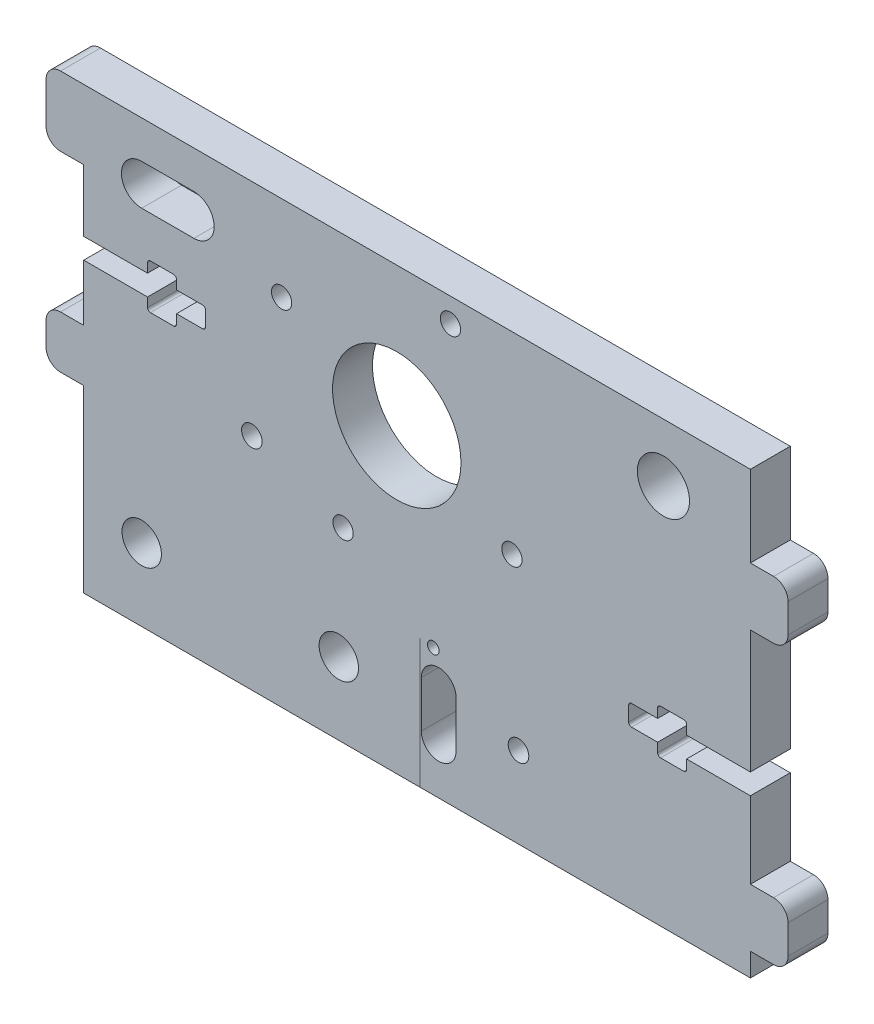
SolidWorks part; units mm, degrees
material "Melamine resin"
ref_plane "Front Plane" through (0, 0, 0) normal (0, 0, 1) x (1, 0, 0)
ref_plane "Top Plane" through (0, 0, 0) normal (0, 1, 0) x (1, 0, 0)
ref_plane "Right Plane" through (0, 0, 0) normal (1, 0, 0) x (0, 0, -1)
sketch "Sketch1" plane through (0, 0, 0) normal (0, 0, 1) x (1, 0, 0)
  line L1 (57.5, 38) -> (-57.5, 38)
  line L2 (57.5, 38) -> (57.5, -38)
  line L3 (57.5, -38) -> (-57.5, -38)
  line L4 (-57.5, 38) -> (-57.5, -38)
  line L5 (57.5, 38) -> (-57.5, -38) construction
  line L6 (57.5, -38) -> (-57.5, 38) construction
  line L7 (5.7639, 33.8665) -> (-23.3665, 23.2639) construction
  line L8 (5.7639, 33.8665) -> (16.3665, 4.7361) construction
  line L9 (16.3665, 4.7361) -> (-12.7639, -5.8665) construction
  line L10 (-23.3665, 23.2639) -> (-12.7639, -5.8665) construction
  line L11 (5.7639, 33.8665) -> (-12.7639, -5.8665) construction
  line L12 (16.3665, 4.7361) -> (-23.3665, 23.2639) construction
  circle A0 centre (-23.3665, 23.2639) radius 1.75
  circle A1 centre (-3.5, 14) radius 11.075
  circle A2 centre (5.7639, 33.8665) radius 1.75
  circle A3 centre (16.3665, 4.7361) radius 1.75
  circle A4 centre (-12.7639, -5.8665) radius 1.75
  point P0 (0, 0)
  point P5 (-3.5, 14)
  dimension "D1" = 31
  dimension "D2" = 3.5
  dimension "D3" = 22.15
  dimension "D7" = 52
  dimension "D6" = 54
  dimension "D4" = 115
  dimension "D5" = 76
  dimension "D8" = 20
extrude "Boss-Extrude1" add sketch "Sketch1" along normal blind 6.88
sketch "Sketch2" plane through (0, 0, 6.88) normal (0, 0, 1) x (1, 0, 0)
  line L0 (-47.5, -25.5) -> (-13.5, -25.5) construction
  line L1 (-57.5, -38) -> (57.5, -38) construction
  line L2 (-57.5, 38) -> (-57.5, -38) construction
  circle A0 centre (-47.5, -25.5) radius 3.4
  circle A1 centre (-13.5, -25.5) radius 3.4
  dimension "D1" = 6.8
  dimension "D4" = 10
  dimension "D2" = 12.5
  dimension "D3" = 34
extrude "Cut-Extrude1" cut sketch "Sketch2" against normal through all
sketch "Sketch4" plane through (0, 0, 6.88) normal (0, 0, 1) x (1, 0, 0)
  line L0 (-47.5, -25.5) -> (-66.0382, -25.5) construction
  line L1 (-66.0382, 2.9858) -> (-22.2006, 2.9858) construction
  circle A0 centre (17.5, -24) radius 1.775
  circle A1 centre (17.5, -24) radius 12.7 construction
  circle A3 centre (-28.5, 0) radius 1.775
  circle A4 centre (-13.5, -25.5) radius 3.4 construction
  dimension "D1" = 3.55
  dimension "D2" = 25.4
  dimension "D4" = 24
  dimension "D6" = 1.5
  dimension "D3" = 31
  dimension "D5" = 46
extrude "Cut-Extrude3" cut sketch "Sketch4" against normal through all
sketch "Sketch6" plane through (0, 0, 6.88) normal (0, 0, 1) x (1, 0, 0)
  line L0 (57.5, -38) -> (57.5, 38) construction
  line L1 (51, 14) -> (64, 14)
  line L2 (51, 14) -> (51, 24)
  line L3 (51, 24) -> (64, 24)
  line L4 (64, 14) -> (64, 24)
  line L5 (51, 14) -> (64, 24) construction
  line L6 (51, 24) -> (64, 14) construction
  line L7 (-57.5, -38) -> (57.5, -38) construction
  line L9 (45, -34) -> (64, -34)
  line L10 (45, -34) -> (45, -24)
  line L11 (45, -24) -> (64, -24)
  line L12 (64, -34) -> (64, -24)
  point P0 (57.5, 19)
  dimension "D1" = 6.5
  dimension "D2" = 10
  dimension "D4" = 10
  dimension "D5" = 4
extrude "Boss-Extrude2" add sketch "Sketch6" against normal up to surface (6.88 mm away) up to face at (-26.725, 0, 0)
sketch "Sketch7" plane through (0, 0, 6.88) normal (0, 0, 1) x (1, 0, 0)
  line L0 (57.5, 24) -> (57.5, 38) construction
  line L1 (78.5, -10.775) -> (36.5, -10.775)
  line L2 (78.5, -10.775) -> (78.5, -7.225)
  line L3 (78.5, -7.225) -> (36.5, -7.225)
  line L4 (36.5, -10.775) -> (36.5, -7.225)
  line L5 (78.5, -10.775) -> (36.5, -7.225) construction
  line L6 (78.5, -7.225) -> (36.5, -10.775) construction
  line L7 (57.5, -38) -> (57.5, -34) construction
  line L8 (-57.5, -38) -> (57.5, -38) construction
  point P0 (57.5, -9)
  dimension "D1" = 3.55
  dimension "D2" = 21
  dimension "D3" = 29
extrude "Cut-Extrude4" cut sketch "Sketch7" against normal through all
sketch "Sketch8" plane through (0, 0, 6.88) normal (0, 0, 1) x (1, 0, 0)
  line L0 (36.5, -9) -> (44, -9) construction
  line L1 (36.5, -7.225) -> (36.5, -10.775) construction
  line L2 (57.5, -38) -> (57.5, -34) construction
  line L3 (41.5, -12.86) -> (46.5, -12.86)
  line L4 (41.5, -12.86) -> (41.5, -5.14)
  line L5 (41.5, -5.14) -> (46.5, -5.14)
  line L6 (46.5, -12.86) -> (46.5, -5.14)
  line L7 (41.5, -12.86) -> (46.5, -5.14) construction
  line L8 (41.5, -5.14) -> (46.5, -12.86) construction
  dimension "D1" = 5
  dimension "D2" = 7.72
  dimension "D3" = 11
extrude "Cut-Extrude5" cut sketch "Sketch8" against normal through all
sketch "Sketch9" plane through (0, 0, 6.88) normal (0, 0, 1) x (1, 0, 0)
  line L0 (-57.5, -38) -> (57.5, -38) construction
  line L1 (0.5685, -60.2325) -> (0.4315, -60.2325)
  line L2 (0.5685, -60.2325) -> (0.5685, -15.7675)
  line L3 (0.5685, -15.7675) -> (0.4315, -15.7675)
  line L4 (0.4315, -60.2325) -> (0.4315, -15.7675)
  line L5 (0.5685, -60.2325) -> (0.4315, -15.7675) construction
  line L6 (0.5685, -15.7675) -> (0.4315, -60.2325) construction
  circle A0 centre (-13.5, -25.5) radius 3.4 construction
  point P0 (0.5, -38)
  dimension "D1" = 14
extrude "Cut-Extrude6" cut sketch "Sketch9" against normal blind 0.005
sketch "Sketch10" plane through (0, 0, 6.88) normal (0, 0, 1) x (1, 0, 0)
  line L2 (-57.5, 38) -> (-57.5, -38) construction
  line L8 (-78.5, 15.2928) -> (-36.5, 15.2928)
  line L9 (-78.5, 15.2928) -> (-78.5, 11.7428)
  line L10 (-78.5, 11.7428) -> (-36.5, 11.7428)
  line L11 (-36.5, 15.2928) -> (-36.5, 11.7428)
  line L12 (-78.5, 15.2928) -> (-36.5, 11.7428) construction
  line L13 (-78.5, 11.7428) -> (-36.5, 15.2928) construction
  point P7 (-57.5, 13.5178)
  dimension "D1" = 3.55
  dimension "D2" = 21
extrude "Cut-Extrude7" cut sketch "Sketch10" against normal through all
sketch "Sketch11" plane through (0, 0, 6.88) normal (0, 0, 1) x (1, 0, 0)
  line L0 (-57.5, 13.5178) -> (-44, 13.5178) construction
  line L1 (-57.5, 38) -> (-57.5, 15.2928) construction
  line L2 (-46.5, 17.3778) -> (-41.5, 17.3778)
  line L3 (-46.5, 17.3778) -> (-46.5, 9.6578)
  line L4 (-46.5, 9.6578) -> (-41.5, 9.6578)
  line L5 (-41.5, 17.3778) -> (-41.5, 9.6578)
  line L6 (-46.5, 17.3778) -> (-41.5, 9.6578) construction
  line L7 (-46.5, 9.6578) -> (-41.5, 17.3778) construction
  dimension "D1" = 7.72
  dimension "D2" = 5
  dimension "D3" = 11
extrude "Cut-Extrude8" cut sketch "Sketch11" against normal through all
fillet "Fillet1" radius 0.5 12 edges at (36.5, -10.775, 3.44) (41.5, -12.86, 3.44) (36.5, -7.225, 3.44) (41.5, -5.14, 3.44) (46.5, -12.86, 3.44) (46.5, -5.14, 3.44) (-41.5, 17.3778, 3.44) (-41.5, 9.6578, 3.44) (-36.5, 11.7428, 3.44) (-46.5, 9.6578, 3.44) (-46.5, 17.3778, 3.44) (-36.5, 15.2928, 3.44)
sketch "Sketch13" plane through (0, 0, 6.88) normal (0, 0, 1) x (1, 0, 0)
  line L0 (3.7315, -21.5) -> (3.7315, -29.5) construction
  line L1 (6.7315, -21.5) -> (6.7315, -29.5)
  line L2 (0.7315, -21.5) -> (0.7315, -29.5)
  line L3 (-13.5, -25.5) -> (3.7315, -25.5) construction
  line L4 (0.4315, -38) -> (0.4315, -15.7675) construction
  arc A0 (6.7315, -21.5) -> (0.7315, -21.5) centre (3.7315, -21.5) ccw
  arc A1 (0.7315, -29.5) -> (6.7315, -29.5) centre (3.7315, -29.5) ccw
  point P2 (3.7315, -25.5)
  dimension "D1" = 6
  dimension "D2" = 8
  dimension "D3" = 0.3
extrude "Cut-Extrude10" cut sketch "Sketch13" against normal through all
sketch "Sketch14" plane through (0, 0, 6.88) normal (0, 0, 1) x (1, 0, 0)
  line L0 (-57.5, 11.7428) -> (-57.5, -38) construction
  line L1 (-57.5, 38) -> (-64, 38)
  line L2 (-57.5, 38) -> (-57.5, 26)
  line L3 (-57.5, 26) -> (-64, 26)
  line L4 (-64, 38) -> (-64, 26)
  line L5 (-57.5, 2) -> (-64, 2)
  line L6 (-57.5, 2) -> (-57.5, -7)
  line L7 (-57.5, -7) -> (-64, -7)
  line L8 (-64, 2) -> (-64, -7)
  dimension "D1" = 6.5
  dimension "D2" = 12
  dimension "D3" = 24
  dimension "D4" = 9
extrude "Boss-Extrude3" add sketch "Sketch14" against normal up to surface (6.88 mm away) up to face at (3.7315, -25.5, 0)
sketch "Sketch15" plane through (0, 0, 6.88) normal (0, 0, 1) x (1, 0, 0)
  line L0 (-47.5, 28) -> (-38.5, 28) construction
  line L1 (-47.5, 31.5) -> (-38.5, 31.5)
  line L2 (-47.5, 24.5) -> (-38.5, 24.5)
  line L3 (-57.5, 26) -> (-57.5, 15.2928) construction
  line L4 (57.5, 38) -> (-64, 38) construction
  line L5 (57.5, 24) -> (57.5, 38) construction
  arc A0 (-47.5, 31.5) -> (-47.5, 24.5) centre (-47.5, 28) ccw
  arc A1 (-38.5, 24.5) -> (-38.5, 31.5) centre (-38.5, 28) ccw
  circle A2 centre (42.5, 28) radius 4.5
  point P2 (-43, 28)
  dimension "D3" = 9
  dimension "D4" = 10
  dimension "D1" = 9
  dimension "D2" = 7
  dimension "D5" = 10
  dimension "D6" = 15
extrude "Cut-Extrude11" cut sketch "Sketch15" against normal through all
fillet "Fillet2" radius 2.5 8 edges at (64, -34, 3.44) (64, -24, 3.44) (64, 14, 3.44) (64, 24, 3.44) (-64, -7, 3.44) (-64, 2, 3.44) (-64, 26, 3.44) (-64, 38, 3.44)
sketch "Sketch16" plane through (0, 0, 6.88) normal (0, 0, 1) x (1, 0, 0)
  text T0 "SeeMeCNC \r\n87907  R1" font "1CamBam_Stick_9" height 2.5
sketch "Sketch17" plane through (0, 0, 6.88) normal (0, 0, 1) x (1, 0, 0)
  line L0 (-13.5, -25.5) -> (4.3943, -25.5) construction
  circle A0 centre (2.8058, -16) radius 1
  circle A1 centre (2.8058, -16) radius 2.7 construction
  dimension "D1" = 2
  dimension "D2" = 5.4
  dimension "D3" = 19
extrude "Cut-Extrude12" cut sketch "Sketch17" against normal through all
equation "\"22.1000mm..05\"=22.1"
